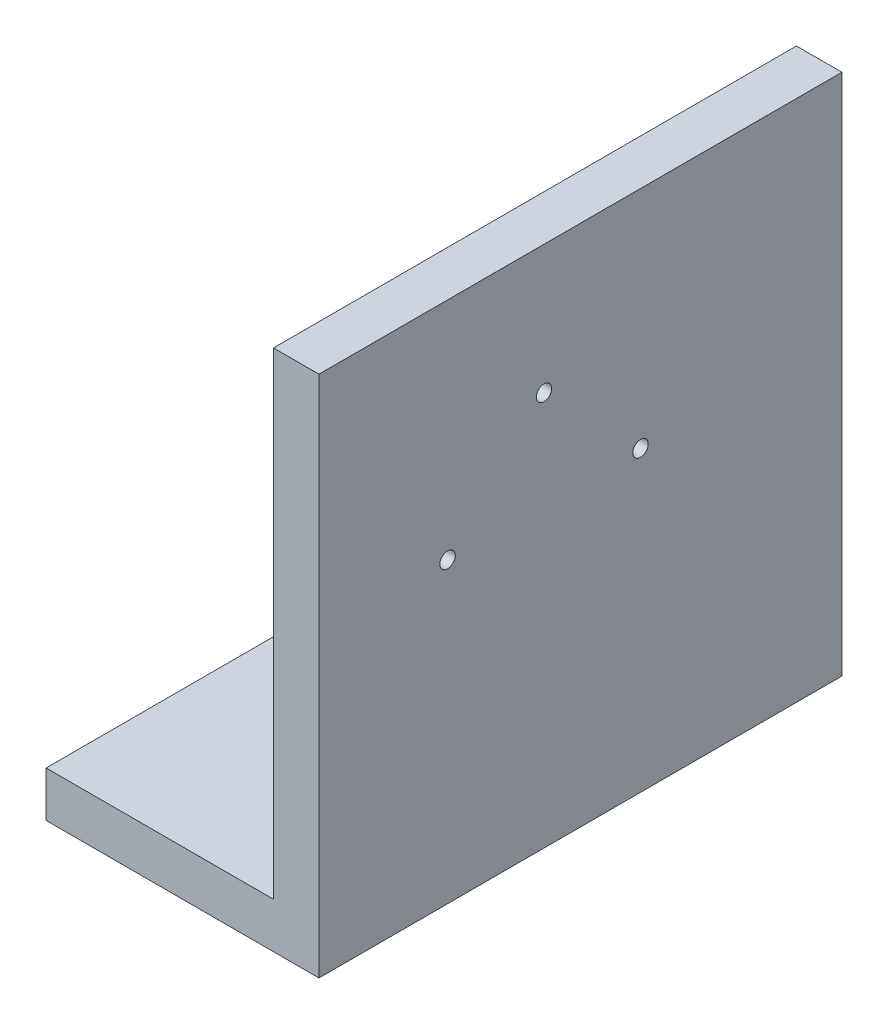
SolidWorks part; units mm, degrees
ref_plane "Plano frontal" through (0, 0, 0) normal (0, 0, 1) x (1, 0, 0)
ref_plane "Plano superior" through (0, 0, 0) normal (0, 1, 0) x (1, 0, 0)
ref_plane "Plano direito" through (0, 0, 0) normal (1, 0, 0) x (0, 0, -1)
sketch "Sketch1" plane through (-23545.4736, 0, 0) normal (-1, 0, 0) x (0, 0, 1)
  line L1 (40286.9363, 5976.6902) -> (40056.9363, 5976.6902)
  line L2 (40286.9363, 5976.6902) -> (40286.9363, 5746.6902)
  line L3 (40286.9363, 5746.6902) -> (40056.9363, 5746.6902)
  line L4 (40056.9363, 5976.6902) -> (40056.9363, 5746.6902)
  dimension "D1" = 230
extrude "Boss-Extrude1" add sketch "Sketch1" along normal blind 20
sketch "Sketch2" plane through (-23565.4736, 0, 0) normal (-1, 0, 0) x (0, 0, 1)
  circle A0 centre (40187.9413, 5920.1217) radius 3.4
  circle A1 centre (40230.3677, 5877.6953) radius 3.4
  circle A2 centre (40145.5149, 5877.6953) radius 3.4
  circle A3 centre (40145.5149, 5877.6953) radius 3.4 construction
  circle A4 centre (40187.9413, 5920.1217) radius 3.4 construction
  circle A5 centre (40230.3677, 5877.6953) radius 3.4 construction
extrude "Cut-Extrude1" cut sketch "Sketch2" against normal through all
sketch "Sketch3" plane through (-23565.4736, 0, 0) normal (-1, 0, 0) x (0, 0, 1)
  line L0 (40056.9363, 5746.6902) -> (40286.9363, 5746.6902) construction
  line L1 (40056.9363, 5766.6902) -> (40286.9363, 5766.6902)
  line L2 (40056.9363, 5766.6902) -> (40056.9363, 5746.6902)
  line L3 (40056.9363, 5746.6902) -> (40286.9363, 5746.6902)
  line L4 (40286.9363, 5766.6902) -> (40286.9363, 5746.6902)
  line L5 (40286.9363, 5746.6902) -> (40286.9363, 5976.6902) construction
  point P4 (40076.7619, 5765.5151)
  point P7 (0, 0)
  point P8 (0, 0)
  point P9 (0, 0)
  point P10 (40216.9736, 5766.6902)
  point P11 (0, 0)
  point P13 (0, 0)
  point P14 (0, 0)
  dimension "D1" = 20
extrude "Boss-Extrude2" add sketch "Sketch3" along normal blind 100
